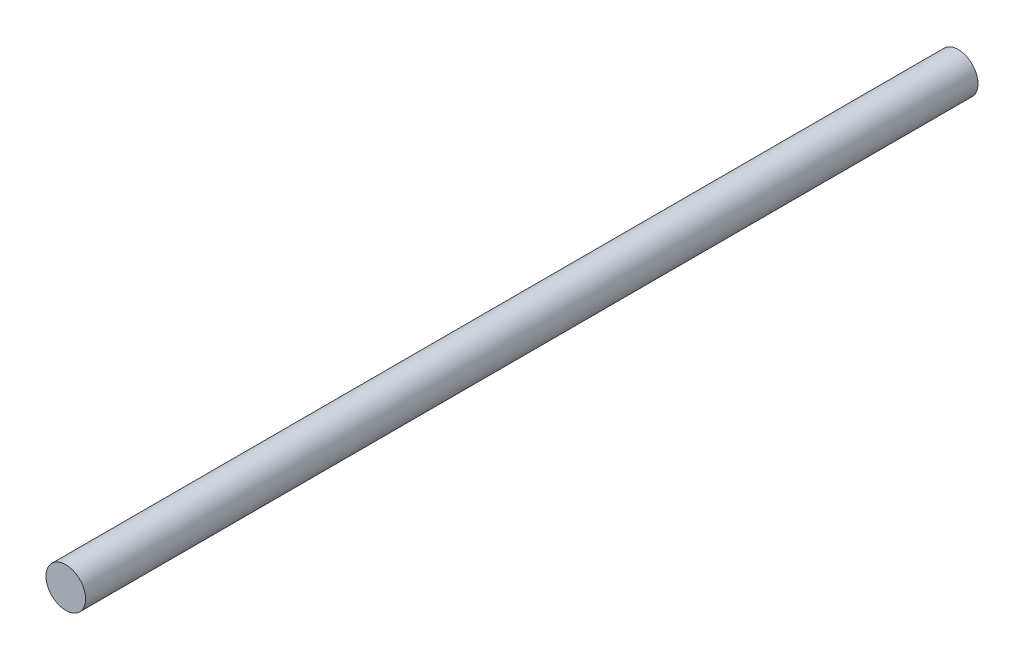
SolidWorks part; units mm, degrees
ref_plane "Alzado" through (0, 0, 0) normal (0, 0, 1) x (1, 0, 0)
ref_plane "Planta" through (0, 0, 0) normal (0, 1, 0) x (1, 0, 0)
ref_plane "Vista lateral" through (0, 0, 0) normal (1, 0, 0) x (0, 0, -1)
sketch "Croquis1" plane through (0, 0, 0) normal (0, 0, 1) x (1, 0, 0)
  circle A0 centre (0, 0) radius 10
  dimension "D1" = 20
extrude "Saliente-Extruir1" add sketch "Croquis1" along normal blind 450
